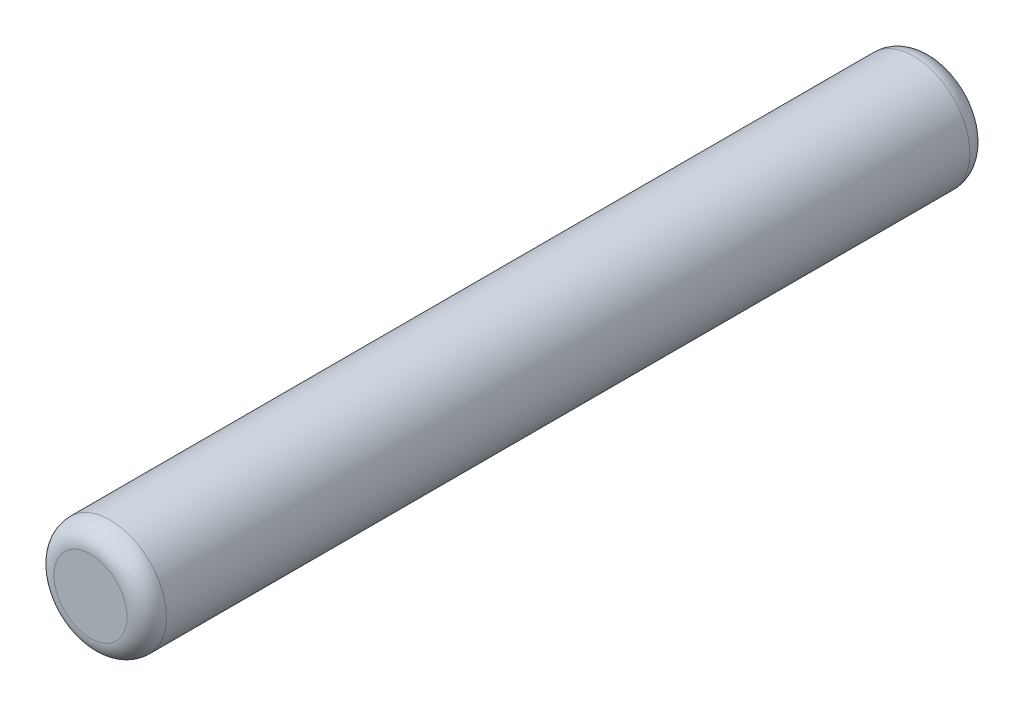
SolidWorks part; units mm, degrees
ref_plane "Front" through (0, 0, 0) normal (0, 0, 1) x (1, 0, 0)
ref_plane "Top" through (0, 0, 0) normal (0, 1, 0) x (1, 0, 0)
ref_plane "Right" through (0, 0, 0) normal (1, 0, 0) x (0, 0, -1)
sketch "Sketch1" plane through (0, 0, 0) normal (0, 0, 1) x (1, 0, 0)
  circle A0 centre (0, 0) radius 1
  dimension "D1" = 2
extrude "Boss-Extrude1" add sketch "Sketch1" along normal mid plane 15
fillet "Fillet1" radius 0.35 2 edges at (1, 0, -7.5) (1, 0, 7.5)
